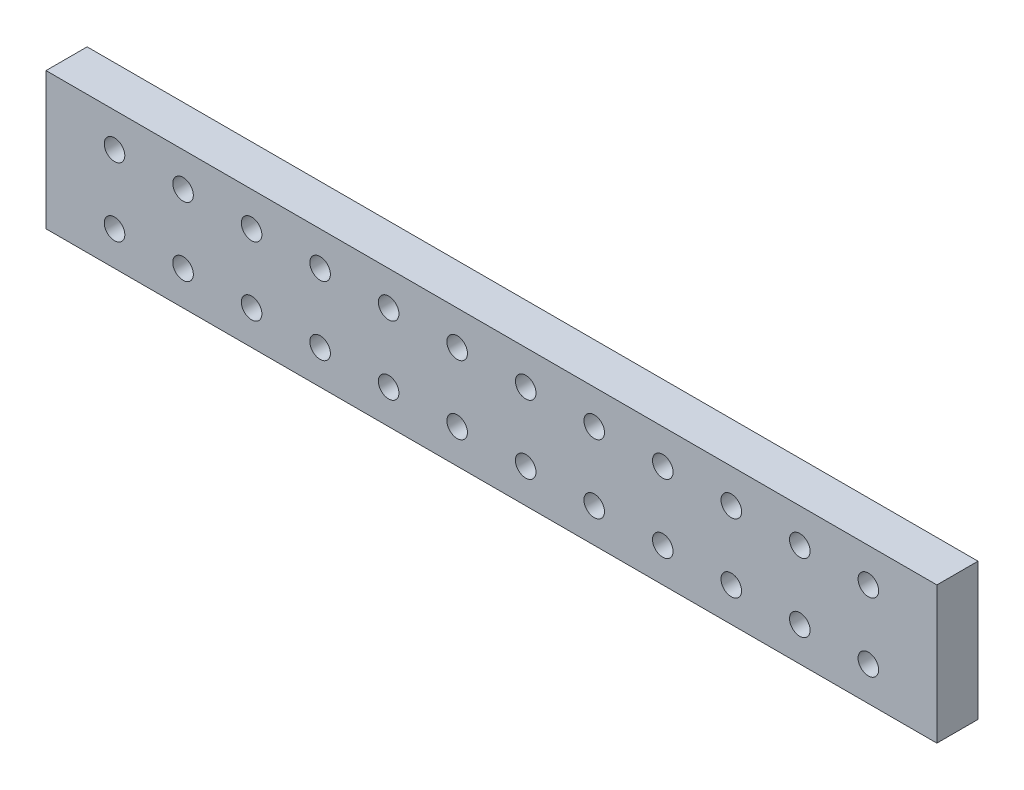
SolidWorks part; units mm, degrees
ref_plane "Front Plane" through (0, 0, 0) normal (0, 0, 1) x (1, 0, 0)
ref_plane "Top Plane" through (0, 0, 0) normal (0, 1, 0) x (1, 0, 0)
ref_plane "Right Plane" through (0, 0, 0) normal (1, 0, 0) x (0, 0, -1)
sketch "Sketch1" plane through (0, 0, 0) normal (0, 0, 1) x (1, 0, 0)
  line L0 (-60.7339, 1.8349) -> (69.2661, 1.8349) construction
  line L1 (-60.7339, 11.8349) -> (69.2661, 11.8349)
  line L2 (-60.7339, 11.8349) -> (-60.7339, -8.1651)
  line L3 (-60.7339, -8.1651) -> (69.2661, -8.1651)
  line L4 (69.2661, 11.8349) -> (69.2661, -8.1651)
  line L5 (69.2661, 9.2661) -> (59.2661, 9.2661) construction
  line L6 (59.2661, 9.2661) -> (59.2661, -8.1651) construction
  line L7 (-60.7339, -8.1651) -> (69.2661, 11.8349) construction
  line L8 (4.2661, 11.8349) -> (4.2661, -8.1651) construction
  line L9 (59.2661, 6.8349) -> (49.2661, 6.8349) construction
  line L10 (49.2661, 6.8349) -> (39.2661, 6.8349) construction
  line L11 (39.2661, 6.8349) -> (29.2661, 6.8349) construction
  line L12 (29.2661, 6.8349) -> (19.2661, 6.8349) construction
  line L13 (19.2661, 6.8349) -> (9.2661, 6.8349) construction
  circle A0 centre (59.2661, -3.1651) radius 1.5
  circle A1 centre (59.2661, 6.8349) radius 1.5
  circle A2 centre (-50.7339, -3.1651) radius 1.5
  circle A3 centre (-50.7339, 6.8349) radius 1.5
  circle A4 centre (49.2661, 6.8349) radius 1.5
  circle A5 centre (39.2661, 6.8349) radius 1.5
  circle A6 centre (29.2661, 6.8349) radius 1.5
  circle A7 centre (19.2661, 6.8349) radius 1.5
  circle A8 centre (9.2661, 6.8349) radius 1.5
  circle A9 centre (49.2661, -3.1651) radius 1.5
  circle A10 centre (39.2661, -3.1651) radius 1.5
  circle A11 centre (29.2661, -3.1651) radius 1.5
  circle A12 centre (19.2661, -3.1651) radius 1.5
  circle A13 centre (9.2661, -3.1651) radius 1.5
  circle A14 centre (-40.7339, -3.1651) radius 1.5
  circle A15 centre (-40.7339, 6.8349) radius 1.5
  circle A16 centre (-30.7339, 6.8349) radius 1.5
  circle A17 centre (-30.7339, -3.1651) radius 1.5
  circle A18 centre (-20.7339, -3.1651) radius 1.5
  circle A19 centre (-20.7339, 6.8349) radius 1.5
  circle A20 centre (-10.7339, 6.8349) radius 1.5
  circle A21 centre (-10.7339, -3.1651) radius 1.5
  circle A22 centre (-0.7339, -3.1651) radius 1.5
  circle A23 centre (-0.7339, 6.8349) radius 1.5
  dimension "D4" = 3
  dimension "D11" = 3
  dimension "D12" = 3
  dimension "D13" = 3
  dimension "D14" = 3
  dimension "D15" = 3
  dimension "D1" = 20
  dimension "D2" = 130
  dimension "D3" = 10
  dimension "D5" = 5
  dimension "D6" = 10
  dimension "D7" = 10
  dimension "D8" = 10
  dimension "D9" = 10
  dimension "D10" = 10
extrude "Boss-Extrude1" add sketch "Sketch1" along normal blind 6
